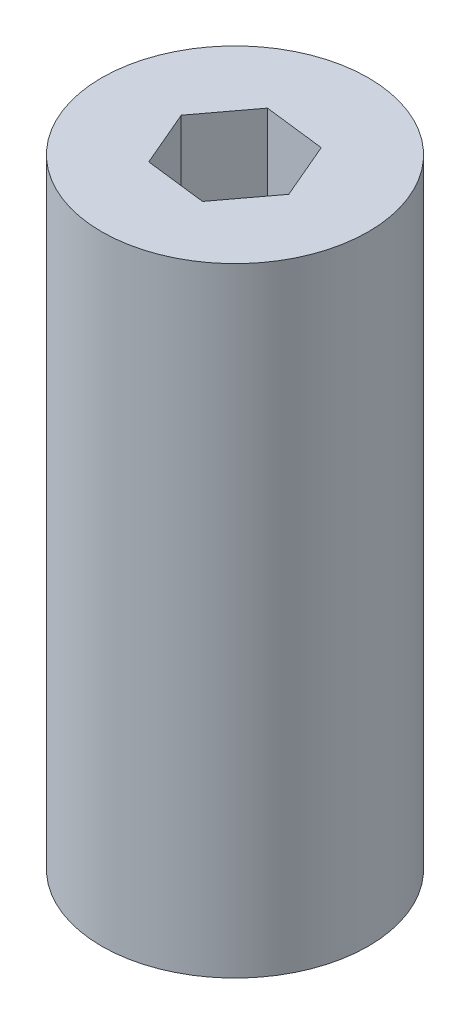
SolidWorks part; units mm, degrees
ref_plane "Front Plane" through (0, 0, 0) normal (0, 0, 1) x (1, 0, 0)
ref_plane "Top Plane" through (0, 0, 0) normal (0, 1, 0) x (1, 0, 0)
ref_plane "Right Plane" through (0, 0, 0) normal (1, 0, 0) x (0, 0, -1)
sketch "Sketch1" plane through (0, 0, 0) normal (0, 1, 0) x (1, 0, 0)
  line L1 (4.3994, 5.8659) -> (-2.8803, 6.7429)
  line L2 (-2.8803, 6.7429) -> (-7.2797, 0.8771)
  line L3 (-7.2797, 0.8771) -> (-4.3994, -5.8659)
  line L4 (-4.3994, -5.8659) -> (2.8803, -6.7429)
  line L5 (2.8803, -6.7429) -> (7.2797, -0.8771)
  line L6 (7.2797, -0.8771) -> (4.3994, 5.8659)
  circle A0 centre (0, 0) radius 15.875
  circle A1 centre (0, 0) radius 6.35 construction
  dimension "D1" = 31.75
  dimension "D2" = 12.7
extrude "Boss-Extrude1" add sketch "Sketch1" along normal blind 73.66
